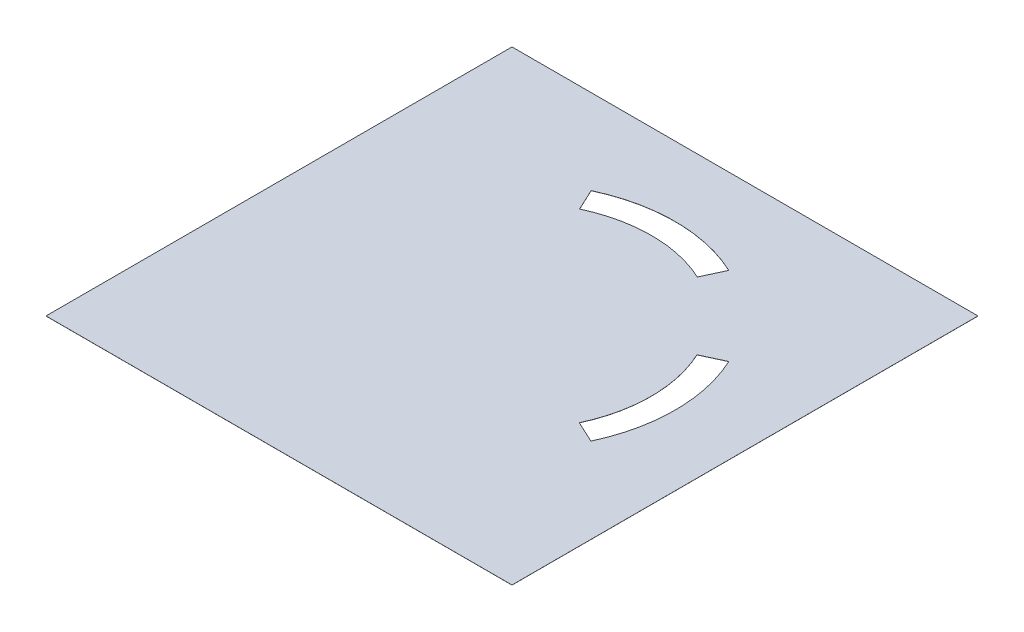
SolidWorks part; units mm, degrees
ref_plane "Front Plane" through (0, 0, 0) normal (0, 0, 1) x (1, 0, 0)
ref_plane "Top Plane" through (0, 0, 0) normal (0, 1, 0) x (1, 0, 0)
ref_plane "Right Plane" through (0, 0, 0) normal (1, 0, 0) x (0, 0, -1)
sketch "Sketch1" plane through (0, 0, 0) normal (0, 1, 0) x (1, 0, 0)
  line L0 (0, 0) -> (0, 107.07)
  line L1 (0, 0) -> (107.07, 0)
  line L2 (0, 107.07) -> (107.07, 107.07)
  line L3 (107.07, 107.07) -> (107.07, 0)
  line L10 (40.021, 82.5764) -> (37.6953, 87.5639)
  line L13 (67.0772, 82.5764) -> (69.3747, 87.5034)
  line L14 (82.5187, 67.0503) -> (87.5034, 69.3747)
  line L15 (82.5187, 40.0197) -> (87.5034, 37.6953)
  arc A0 (37.6953, 87.5639) -> (69.3747, 87.5034) centre (53.4708, 53.8846) cw
  arc A1 (40.021, 82.5764) -> (67.0772, 82.5764) centre (53.5491, 53.5652) cw
  arc A2 (82.5187, 67.0503) -> (82.5187, 40.0197) centre (53.535, 53.535) cw
  arc A3 (87.5034, 69.3747) -> (87.5034, 37.6953) centre (53.535, 53.535) cw
extrude "Boss-Extrude1" add sketch "Sketch1" along normal blind 0.02
